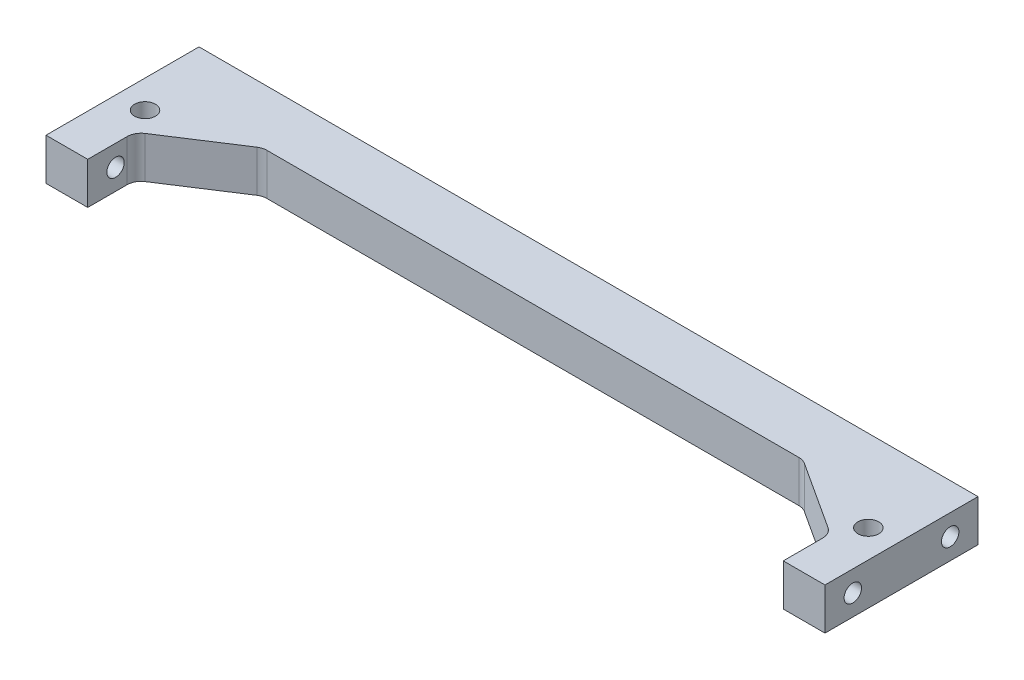
SolidWorks part; units mm, degrees
ref_plane "Front Plane" through (0, 0, 0) normal (0, 0, 1) x (1, 0, 0)
ref_plane "Top Plane" through (0, 0, 0) normal (0, 1, 0) x (1, 0, 0)
ref_plane "Right Plane" through (0, 0, 0) normal (1, 0, 0) x (0, 0, -1)
sketch "Sketch1" plane through (0, 0, 0) normal (0, 1, 0) x (1, 0, 0)
  line L1 (0, -22) -> (-56, -22)
  line L2 (-56, -22) -> (-56, -44)
  line L3 (-50, -37.2398) -> (-38.8516, -30)
  line L4 (0, -30) -> (0, -22)
  line L5 (0, -30) -> (-38.8516, -30)
  line L6 (-56, -44) -> (-50, -44)
  line L7 (-51.9976, -33.7676) -> (-63.9796, -15.3169) construction
  line L8 (-50, -44) -> (-50, -37.2398)
  line L9 (0, 0) -> (-85, 0) construction
  line L10 (-43.8406, 43.8406) -> (0, 0) construction
  line L11 (-51.9976, -33.7676) -> (0, 0) construction
  line L24 (-54.4746, -32.0752) -> (-40.5, -23) construction
  line L25 (-50, 65) -> (-20, 80) construction
  line L26 (-20, 80) -> (0, 80) construction
  line L27 (0, 80) -> (0, 4) construction
  line L28 (0, 4) -> (-50, 4) construction
  line L29 (-50, 65) -> (-50, 4) construction
  circle A0 centre (0, 0) radius 85 construction
  circle A1 centre (-51.9976, -33.7676) radius 3 construction
  circle A2 centre (-51.9976, -33.7676) radius 1.5
  circle A4 centre (-63.9796, -15.3169) radius 1.5 construction
  dimension "D7" = 6
  dimension "D17" = 170
  dimension "D6" = 6
  dimension "D13" = 3
  dimension "D2" = 30
  dimension "D4" = 4
  dimension "D5" = 2.7685
  dimension "D8" = 62
  dimension "D9" = 56
  dimension "D10" = 22
  dimension "D11" = 8
  dimension "D12" = 22
  dimension "D14" = 45
  dimension "D15" = 33
  dimension "D29" = 50
  dimension "D30" = 30
  dimension "D31" = 15
  dimension "D32" = 80
  dimension "D33" = 76
extrude "Boss-Extrude1" add sketch "Sketch1" along normal blind 6
fillet "Fillet1" radius 2 2 edges at (-50, 3, 37.2398) (-38.8516, 3, 30)
hole_wizard "Tap Drill for M3 Tap1" positions "Sketch3" profile "Sketch2" hole size "M3" standard "ISO"
sketch "Sketch3" plane through (-56, 0, 0) normal (-1, 0, 0) x (0, 0, 1)
  line L0 (44, 6) -> (44, 0) construction
  line L1 (22, 0) -> (44, 0) construction
  point P0 (26, 3)
  point P2 (40, 3)
  dimension "D1" = 4
  dimension "D2" = 14
  dimension "D3" = 3
sketch "Sketch2" plane through (-56, 3, 26) normal (0, 1, 0) x (0, 0, 1)
  line L0 (0, 0) -> (0, 10.7511)
  line L1 (0, 10.7511) -> (1.25, 10)
  line L2 (1.25, 10) -> (1.25, 0)
  line L5 (1.25, 0) -> (0, 0)
  line L10 (0, 10.7511) -> (-1.25, 10) construction
  line L11 (0, -6.35) -> (0, 107.95) construction
  dimension "Hole Dia." = 2.5
  dimension "Hole Depth" = 10
  dimension "Drill Angle" = 118
mirror "Mirror1" about plane through (0, 6, 30) normal (-1, 0, 0) of "Tap Drill for M3 Tap1", "Fillet1", "Boss-Extrude1"
